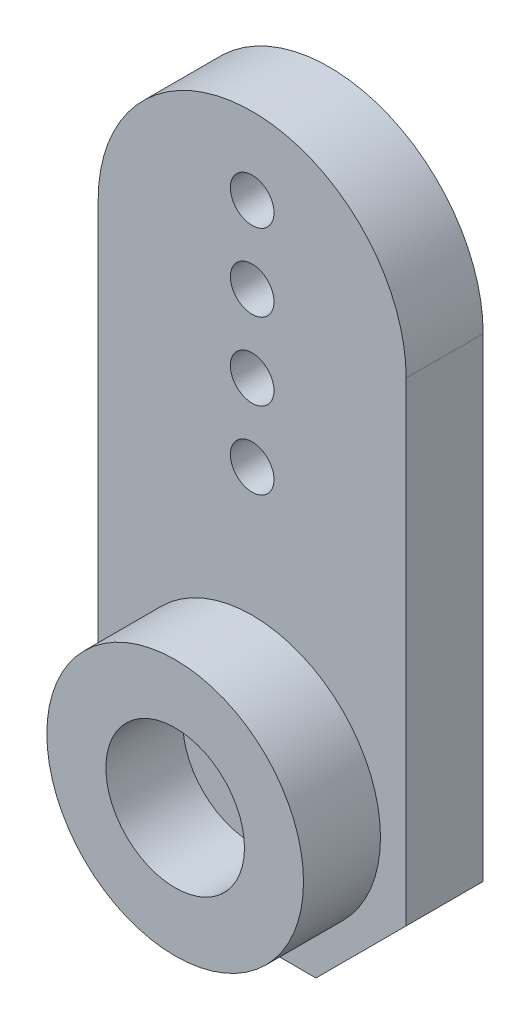
SolidWorks part; units mm, degrees
ref_plane "Спереди" through (0, 0, 0) normal (0, 0, 1) x (1, 0, 0)
ref_plane "Сверху" through (0, 0, 0) normal (0, 1, 0) x (1, 0, 0)
ref_plane "Справа" through (0, 0, 0) normal (1, 0, 0) x (0, 0, -1)
sketch "Эскиз1" plane through (0, 0, 0) normal (0, 0, 1) x (1, 0, 0)
  line L0 (6, 16) -> (6, -2.4853)
  line L1 (6, -2.4853) -> (2.4853, -6)
  line L2 (2.4853, -6) -> (-2.4853, -6)
  line L3 (-2.4853, -6) -> (-6, -2.4853)
  line L4 (-6, -2.4853) -> (-6, 16)
  arc A0 (-6, 16) -> (6, 16) centre (0, 16) cw
  circle A1 centre (0, 0) radius 1.35
  circle A2 centre (0, 10) radius 0.85
  circle A3 centre (0, 13) radius 0.85
  circle A4 centre (0, 16) radius 0.85
  circle A5 centre (0, 19) radius 0.85
  point P18 (0, 0)
  dimension "D3" = 16
  dimension "D6" = 2.7
  dimension "D7" = 1.7
  dimension "D8" = 19
  dimension "D9" = 3
  dimension "D10" = 3
  dimension "D11" = 3
  dimension "D1" = 45
  dimension "D2" = 6
  dimension "D4" = 12
  dimension "D5" = 6
extrude "Бобышка-Вытянуть1" add sketch "Эскиз1" along normal blind 3
sketch "Эскиз2" plane through (0, 0, 3) normal (0, 0, 1) x (1, 0, 0)
  circle A0 centre (0, 0) radius 2.7
  circle A1 centre (0, 0) radius 5
  dimension "D1" = 10
  dimension "D2" = 5.4
extrude "Бобышка-Вытянуть2" add sketch "Эскиз2" along normal blind 3
sketch "Эскиз3" plane through (0, 0, 0) normal (0, 0, -1) x (-1, 0, 0)
  circle A0 centre (0, 0) radius 3
  dimension "D1" = 6
extrude "Вырез-Вытянуть1" cut sketch "Эскиз3" against normal blind 1.5
